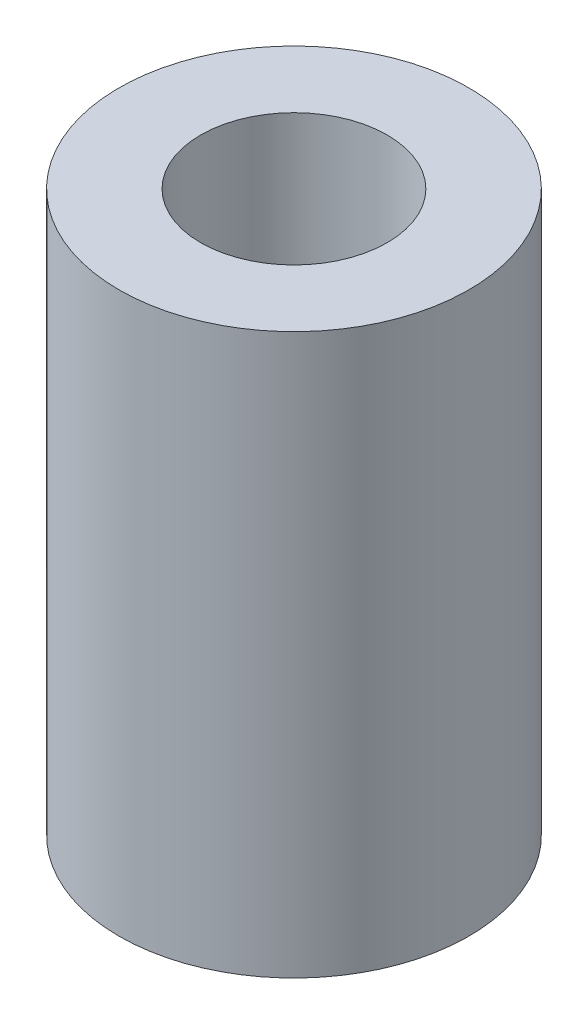
SolidWorks part; units mm, degrees
material "AISI 304"
ref_plane "Front Plane" through (0, 0, 0) normal (0, 0, 1) x (1, 0, 0)
ref_plane "Top Plane" through (0, 0, 0) normal (0, 1, 0) x (1, 0, 0)
ref_plane "Right Plane" through (0, 0, 0) normal (1, 0, 0) x (0, 0, -1)
sketch "Sketch1" plane through (0, 0, 0) normal (0, 1, 0) x (1, 0, 0)
  circle A0 centre (0, 0) radius 7.5
  circle A1 centre (0, 0) radius 4
  dimension "D1" = 8
  dimension "D2" = 15
extrude "Boss-Extrude1" add sketch "Sketch1" along normal blind 24
